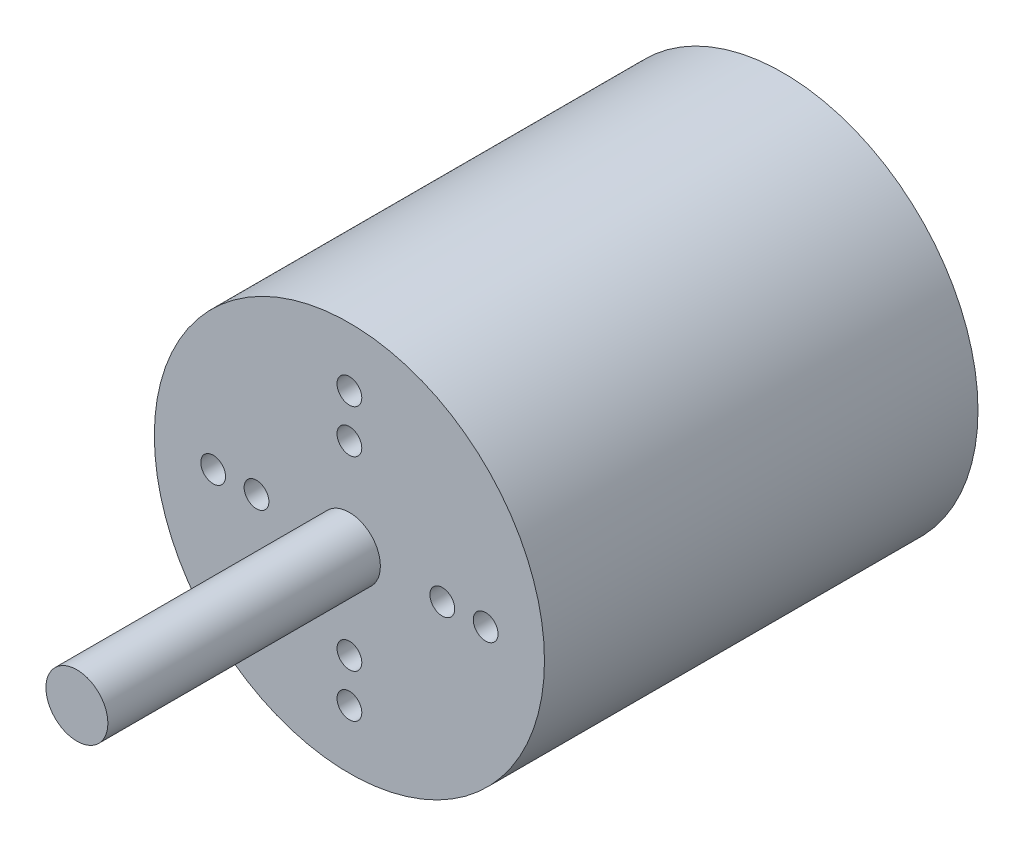
SolidWorks part; units mm, degrees
ref_plane "Front Plane" through (0, 0, 0) normal (0, 0, 1) x (1, 0, 0)
ref_plane "Top Plane" through (0, 0, 0) normal (0, 1, 0) x (1, 0, 0)
ref_plane "Right Plane" through (0, 0, 0) normal (1, 0, 0) x (0, 0, -1)
sketch "Sketch1" plane through (0, 0, 0) normal (0, 0, 1) x (1, 0, 0)
  circle A0 centre (0, 0) radius 31.5
  dimension "D1" = 63
extrude "Boss-Extrude1" add sketch "Sketch1" against normal blind 70
sketch "Sketch2" plane through (0, 0, 0) normal (0, 0, 1) x (1, 0, 0)
  circle A0 centre (0, 0) radius 5
  dimension "D1" = 10
extrude "Boss-Extrude2" add sketch "Sketch2" along normal blind 44
sketch "Sketch5" plane through (0, 0, -70) normal (0, 0, -1) x (-1, 0, 0)
  circle A0 centre (0, 0) radius 11 construction
  circle A1 centre (-11, 0) radius 2
  dimension "D1" = 22
  dimension "D2" = 4
extrude "Cut-Extrude2" cut sketch "Sketch5" against normal blind 10
sketch "Sketch6" plane through (0, 0, 0) normal (0, 0, 1) x (1, 0, 0)
  circle A0 centre (0, 0) radius 15 construction
  circle A1 centre (0, 15) radius 2
  circle A5 centre (0, 0) radius 22 construction
  circle A6 centre (0, 22) radius 2
  dimension "D1" = 4
  dimension "D2" = 44
  dimension "D3" = 4
  dimension "D5" = 30
extrude "Cut-Extrude3" cut sketch "Sketch6" against normal blind 5
pattern_circular "CirPattern1" count 4 over 360 about axis through (0, 0, 0) along (0, 0, 1) of "Cut-Extrude3"
pattern_circular "CirPattern2" count 4 over 360 about axis through (0, 0, 0) along (0, 0, 1) of "Cut-Extrude2"
